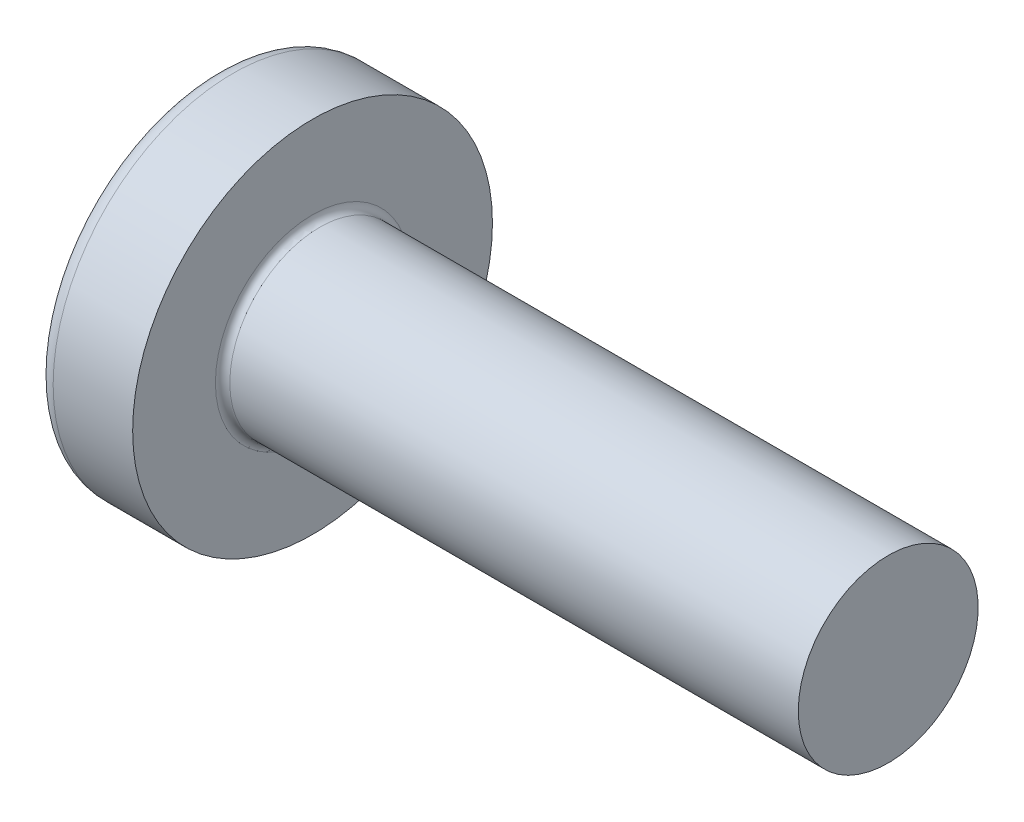
SolidWorks part; units mm, degrees
ref_plane "Plane1" through (0, 0, 0) normal (0, 0, 1) x (1, 0, 0)
ref_plane "Plane2" through (0, 0, 0) normal (0, 1, 0) x (1, 0, 0)
ref_plane "Plane3" through (0, 0, 0) normal (1, 0, 0) x (0, 0, -1)
sketch "BodySke" plane through (0, 0, 0) normal (0, 0, 1) x (1, 0, 0)
  line L0 (2.1, 1.25) -> (2.1, 2.5)
  line L1 (2.325, 6.35) -> (2.325, -3.175) construction
  line L2 (-25.4, 0) -> (127, 0) construction
  line L3 (10.1, 0) -> (0, 0)
  line L4 (2.1, 1.25) -> (10.1, 1.25)
  line L5 (10.1, 1.25) -> (10.1, 0)
  line L6 (0.995, 2.5) -> (2.1, 2.5)
  line L8 (2.1, 6.35) -> (2.1, -3.175) construction
  arc A0 (0.8032, 2.4043) -> (0, 0) centre (4, 0) ccw
  arc A2 (0.8032, 2.4043) -> (0.995, 2.5) centre (0.995, 2.26) cw
revolve "Base-Revolve" add sketch "BodySke"
cosmetic thread "ThreadCosmetic"
fillet "Fillet1" radius 0.1 1 edges at (2.1, 0, 1.25)
sketch "Sketch3" plane through (0, 0, 0) normal (1, 0, 0) x (0, 0, -1)
  line L0 (0.37, -1.3) -> (-0.37, -1.3)
  line L1 (0.37, -1.3) -> (0.37, 1.3)
  line L2 (-0.37, 1.3) -> (0.37, 1.3)
  line L3 (-0.37, 1.3) -> (-0.37, -1.3)
  dimension "D1" = 0.8
  dimension "D2" = 0.24
ref_plane "Plane4" through (1.5, 0, 0) normal (1, 0, 0) x (0, 0, -1)
sketch "Sketch4" plane through (1.5, 0, 0) normal (1, 0, 0) x (0, 0, -1)
  line L0 (0.37, -0.5521) -> (-0.37, -0.5521)
  line L1 (0.37, -0.5521) -> (0.37, 0.5521)
  line L2 (-0.37, 0.5521) -> (0.37, 0.5521)
  line L3 (-0.37, 0.5521) -> (-0.37, -0.5521)
  dimension "D1" = 0.48
  dimension "D3" = 0.24
loft "Recess" cut profiles "Sketch3", "Sketch4"
pattern_circular "RecPat" count 2 every 90 about axis through (0, 0, 0) along (1, 0, 0) of "Recess"
sketch "RecCorSke" plane through (0, 0, 0) normal (0, 0, 1) x (1, 0, 0)
  line L0 (-3.175, 0) -> (15.875, 0) construction
  line L1 (-25.4, 0) -> (127, 0) construction
  line L2 (0, 0) -> (0, 0.6609)
  line L3 (0, 0.6609) -> (1.5, 0.556)
  line L4 (1.5, 0.556) -> (1.6807, 0)
  line L5 (1.6807, 0) -> (0, 0)
  dimension "Draft_angle" = 4
  dimension "Bottom_angle" = 18
revolve "RecessCore" cut sketch "RecCorSke" angle 360 about L0
sketch "ThdSchSke" plane through (0, 0, 0) normal (0, 0, 1) x (1, 0, 0)
  line L0 (3, -0.9965) -> (2.8225, -1.25)
  line L1 (3, -0.9965) -> (3.1775, -1.25)
  line L2 (3.1775, -1.25) -> (3.1775, -1.5625)
  line L3 (-3.175, 0) -> (5.1513, 0) construction
  line L5 (3.1775, -1.5625) -> (2.8225, -1.5625)
  line L6 (2.8225, -1.5625) -> (2.8225, -1.25)
  dimension "SideAngle" = 55
  dimension "VeeAngle" = 70
revolve "ThreadSchematic" [suppressed] cut sketch "ThdSchSke" angle 360 about L3
pattern_linear "ThdSchPat" [suppressed]
equation "\"D1@Sketch3\" = \"Cross_dia@Sketch3\" / 2"
equation "\"D2@Sketch3\" = \"Cross_width@Sketch3\" / 2"
equation "\"Depth@RecCorSke\" = \"Cross_depth@Plane4\""
equation "\"D1@Sketch4\" = \"Cross_width@Sketch3\""
equation "\"D2@Sketch4\" = \"Cross_dia@Sketch3\" - 2.0 * \"Cross_depth@Plane4\" * tan(26.5  * 0.017453292)"
equation "\"D3@Sketch4\" = \"D1@Sketch4\" / 2"
equation "\"D4@Sketch4\" = \"D2@Sketch4\" / 2"
equation "\"Thread_length@ThreadCosmetic\" = ((sgn( (\"Length@BodySke\" - \"Advance@BodySke\" * 2.0 ) - \"Thread_nom@BodySke\" )-1)*( (\"Length@BodySke\" - \"Advance@BodySke\" * 2.0 ) - \"Thread_nom@BodySke\" ))/-2+ \"Thread_nom@BodySke\""
equation "\"Thread_minor@ThdSchSke\" = \"Thread_minor@ThreadCosmetic\""
equation "\"Diameter@ThdSchSke\" = \"Diameter@BodySke\""
equation "\"Overcut@ThdSchSke\" = \"Diameter@BodySke\" * 1.25"
equation "\"Start@ThdSchSke\" = \"Head_ht@BodySke\" + \"Length@BodySke\" - \"Thread_length@ThreadCosmetic\"  '---Non-countersunk---"
equation "\"Num_threads@ThdSchPat\" = int( \"Thread_length@ThreadCosmetic\" / \"Advance@BodySke\" + 0.999 )  + 1"
equation "\"Advance@ThdSchPat\" = \"Thread_length@ThreadCosmetic\" /  (\"Num_threads@ThdSchPat\" - 1) 'relax it"
